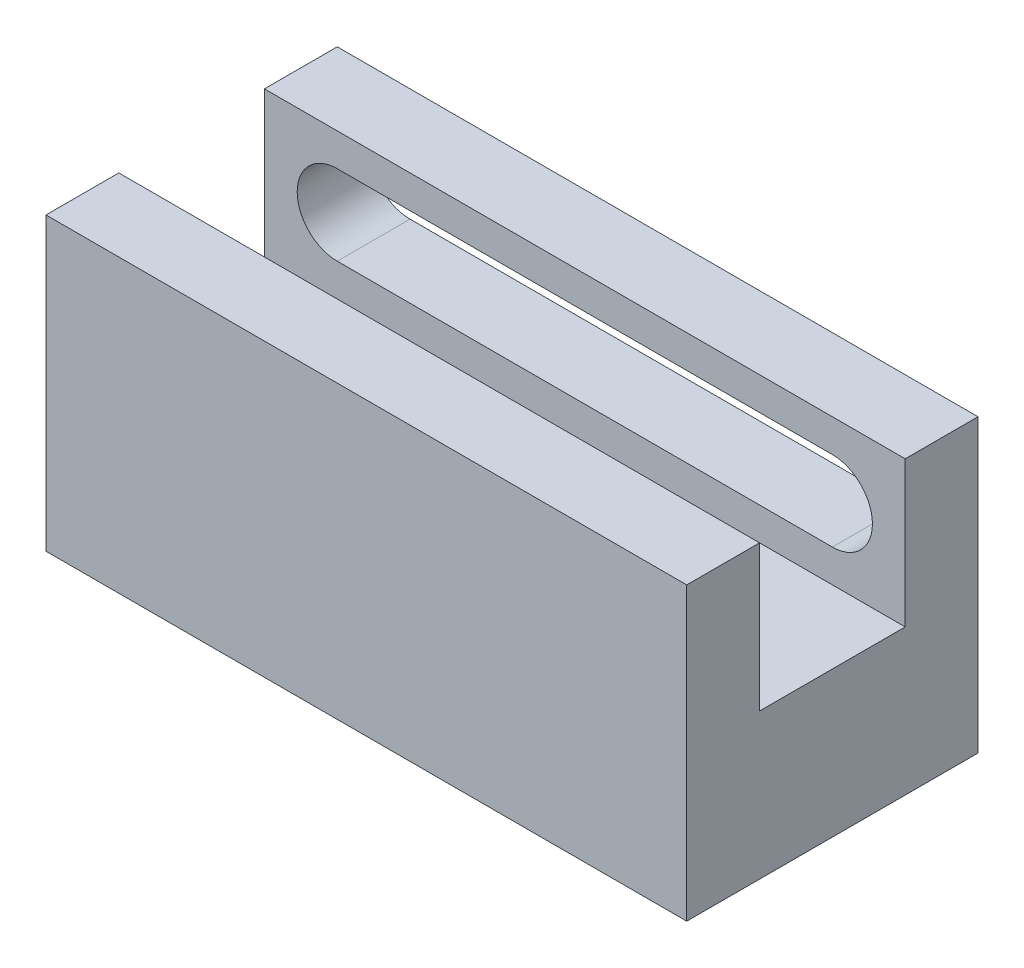
SolidWorks part; units mm, degrees
ref_plane "Front Plane" through (0, 0, 0) normal (0, 0, 1) x (1, 0, 0)
ref_plane "Top Plane" through (0, 0, 0) normal (0, 1, 0) x (1, 0, 0)
ref_plane "Right Plane" through (0, 0, 0) normal (1, 0, 0) x (0, 0, -1)
sketch "Sketch1" plane through (0, 0, 0) normal (0, 1, 0) x (1, 0, 0)
  line L1 (0, 20) -> (44, 20)
  line L2 (0, 20) -> (0, 0)
  line L3 (0, 0) -> (44, 0)
  line L4 (44, 20) -> (44, 0)
  circle A0 centre (22, 10) radius 2.55
  point P8 (22, 20)
  point P10 (44, 10)
  dimension "D3" = 5.1
  dimension "D1" = 44
  dimension "D2" = 20
extrude "Boss-Extrude1" add sketch "Sketch1" along normal blind 7.5
sketch "Sketch2" plane through (0, 7.5, 0) normal (0, 1, 0) x (1, 0, 0)
  line L0 (44, 0) -> (44, 20) construction
  line L1 (44, 0) -> (0, 0)
  line L2 (44, 0) -> (44, 20)
  line L3 (44, 20) -> (0, 20)
  line L4 (0, 0) -> (0, 20)
  line L5 (0, 20) -> (0, 0) construction
  line L6 (44, 20) -> (0, 20) construction
  line L7 (0, 0) -> (44, 0) construction
extrude "Boss-Extrude2" add sketch "Sketch2" along normal blind 2.5
sketch "Sketch3" plane through (0, 10, 0) normal (0, 1, 0) x (1, 0, 0)
  line L0 (0, 0) -> (44, 0) construction
  line L1 (0, 5) -> (44, 5)
  line L2 (0, 5) -> (0, 0)
  line L3 (0, 0) -> (44, 0)
  line L4 (44, 5) -> (44, 0)
  line L5 (44, 0) -> (44, 20) construction
  line L6 (0, 20) -> (0, 0) construction
  line L7 (44, 20) -> (0, 20) construction
  line L8 (44, 15) -> (0, 15)
  line L9 (44, 15) -> (44, 20)
  line L10 (44, 20) -> (0, 20)
  line L11 (0, 15) -> (0, 20)
  dimension "D1" = 5
  dimension "D2" = 5
extrude "Boss-Extrude3" add sketch "Sketch3" along normal blind 10
sketch "Sketch4" plane through (0, 0, -20) normal (0, 0, -1) x (-1, 0, 0)
  line L0 (-44, 20) -> (-44, 0) construction
  line L1 (-39, 17.75) -> (-5, 17.75)
  line L2 (-39, 17.75) -> (-39, 12.25)
  line L3 (-39, 12.25) -> (-5, 12.25)
  line L4 (-5, 17.75) -> (-5, 12.25)
  line L5 (0, 20) -> (0, 0) construction
  line L6 (-44, 20) -> (0, 20) construction
  circle A0 centre (-39, 15) radius 2.75
  circle A1 centre (-5, 15) radius 2.75
  point P6 (-5, 15)
  point P12 (-39, 15)
  dimension "D3" = 5.5
  dimension "D1" = 5
  dimension "D2" = 5
  dimension "D4" = 5
extrude "Cut-Extrude1" cut sketch "Sketch4" against normal blind 5 and the other way through all contours A1 L1 A0 L3 | L2 A0 | L2 A0 | L4 A1 | L4 A1
